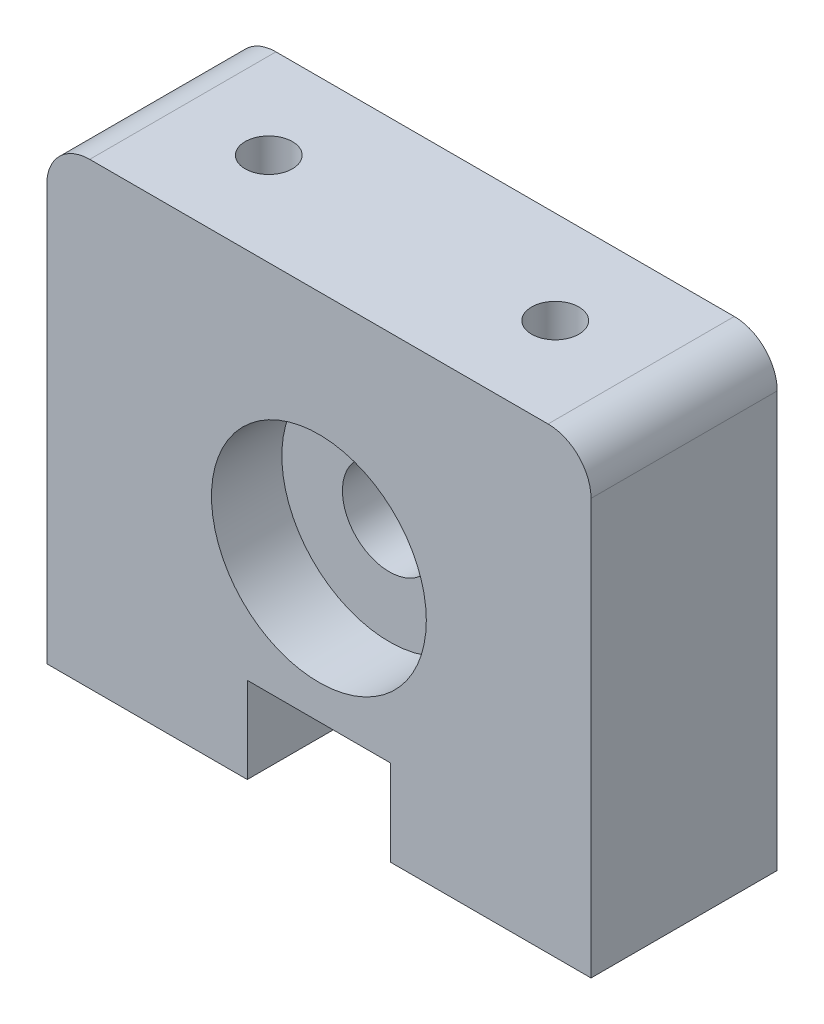
SolidWorks part; units mm, degrees
ref_plane "Front Plane" through (0, 0, 0) normal (0, 0, 1) x (1, 0, 0)
ref_plane "Top Plane" through (0, 0, 0) normal (0, 1, 0) x (1, 0, 0)
ref_plane "Right Plane" through (0, 0, 0) normal (1, 0, 0) x (0, 0, -1)
sketch "Sketch1" plane through (0, 0, 0) normal (0, 0, 1) x (1, 0, 0)
  line L0 (0, -26.1041) -> (0, 52.7781) construction
  line L1 (-16, 32) -> (16, 32)
  line L3 (0, 0) -> (-19, 0)
  line L4 (19, 0) -> (19, 29)
  line L7 (-19, 0) -> (-19, 29)
  line L8 (0, 0) -> (19, 0)
  circle A0 centre (0, 15.874) radius 7.5
  arc A1 (19, 29) -> (16, 32) centre (16, 29) ccw
  arc A2 (-19, 29) -> (-16, 32) centre (-16, 29) cw
  point P5 (19, 32)
  point P10 (-19, 32)
  point P11 (0, 4.699)
  point P12 (0, 28.448)
  point P15 (0, 8.374)
  dimension "D6" = 15
  dimension "D2" = 3
  dimension "D1" = 32
  dimension "D5" = 15.874
  dimension "D7" = 38
extrude "Boss-Extrude1" add sketch "Sketch1" along normal blind 13
ref_plane "Plane1" through (0, 0, 6.5) normal (0, 0, 1) x (1, 0, 0)
sketch "Sketch3" plane through (0, 0, 6.5) normal (0, 0, 1) x (1, 0, 0)
  circle A0 centre (0, 15.874) radius 3.2703
  circle A1 centre (0, 15.874) radius 8.7376
  dimension "D1" = 6.5405
  dimension "D2" = 17.4752
extrude "Boss-Extrude2" add sketch "Sketch3" along normal blind 1.5875 and the other way blind 1.5875
sketch "Sketch7" plane through (0, 0, 0) normal (0, -1, 0) x (1, 0, 0)
  line L0 (-19, 13) -> (19, 0) construction
  line L1 (0, 0) -> (0, 13) construction
  line L2 (-19, 13) -> (19, 13) construction
  point P9 (0, 6.5)
hole_wizard "M4x0.7 Tapped Hole1" positions "Sketch5" profile "Sketch6" tap size "M4x0.7" standard "ANSI Metric"
sketch "Sketch5" plane through (0, 0, 0) normal (0, -1, 0) x (-1, 0, 0)
  point P0 (10, -6.5)
  point P2 (-10, -6.5)
  dimension "D1" = 10
  dimension "D2" = 0
  dimension "D3" = 10
  dimension "D4" = 0
sketch "Sketch6" plane through (-10, 0, 6.5) normal (1, 0, 0) x (0, 0, -1)
  line L0 (0, 0) -> (0, 11.1006)
  line L1 (0, 11.1006) -> (1.65, 10.1092)
  line L2 (1.65, 10.1092) -> (1.65, 0)
  line L5 (1.65, 0) -> (0, 0)
  line L10 (0, 11.1006) -> (-1.65, 10.1092) construction
  line L11 (0, -6.35) -> (0, 107.95) construction
  dimension "Tap Drill Dia." = 3.3
  dimension "Tap Drill Depth" = 10.1092
  dimension "Drill Angle" = 118
cosmetic thread "Hole Thread1" parameters "D1"=8.001, "D2"=4
cosmetic thread "Hole Thread2" parameters "D1"=8.001, "D2"=4
hole_wizard "M4x0.7 Tapped Hole2" positions "Sketch8" profile "Sketch10" tap size "M4x0.7" standard "ANSI Metric"
sketch "Sketch8" plane through (0, 32, 0) normal (0, 1, 0) x (1, 0, 0)
  point P0 (-10, -6.5)
  point P3 (10, -6.5)
sketch "Sketch10" plane through (-10, 32, 6.5) normal (1, 0, 0) x (0, 0, 1)
  line L0 (0, 0) -> (0, 10.9914)
  line L1 (0, 10.9914) -> (1.65, 10)
  line L2 (1.65, 10) -> (1.65, 0)
  line L5 (1.65, 0) -> (0, 0)
  line L10 (0, 10.9914) -> (-1.65, 10) construction
  line L11 (0, -6.35) -> (0, 107.95) construction
  dimension "Tap Drill Dia." = 3.3
  dimension "Tap Drill Depth" = 10
  dimension "Drill Angle" = 118
cosmetic thread "Hole Thread3" parameters "D1"=8, "D2"=4
cosmetic thread "Hole Thread4" parameters "D1"=8, "D2"=4
sketch "Sketch11" plane through (0, 0, 13) normal (0, 0, 1) x (1, 0, 0)
  line L0 (-19, 0) -> (19, 0) construction
  line L1 (-5, 0) -> (5, 0)
  line L2 (-5, 0) -> (-5, 6)
  line L3 (-5, 6) -> (5, 6)
  line L4 (5, 0) -> (5, 6)
  line L5 (-7.5, 15.874) -> (-12.56, 15.874) construction
  circle A0 centre (0, 15.874) radius 7.5 construction
  point P6 (0, 6)
  point P8 (-7.5, 15.874)
  dimension "D1" = 10
  dimension "D2" = 6
extrude "Cut-Extrude1" cut sketch "Sketch11" against normal blind 15
ref_plane "flat plane" through (0, 15.874, 0) normal (0, 1, 0) x (1, 0, 0)
equation "\"0.095inin\"=0.085"
